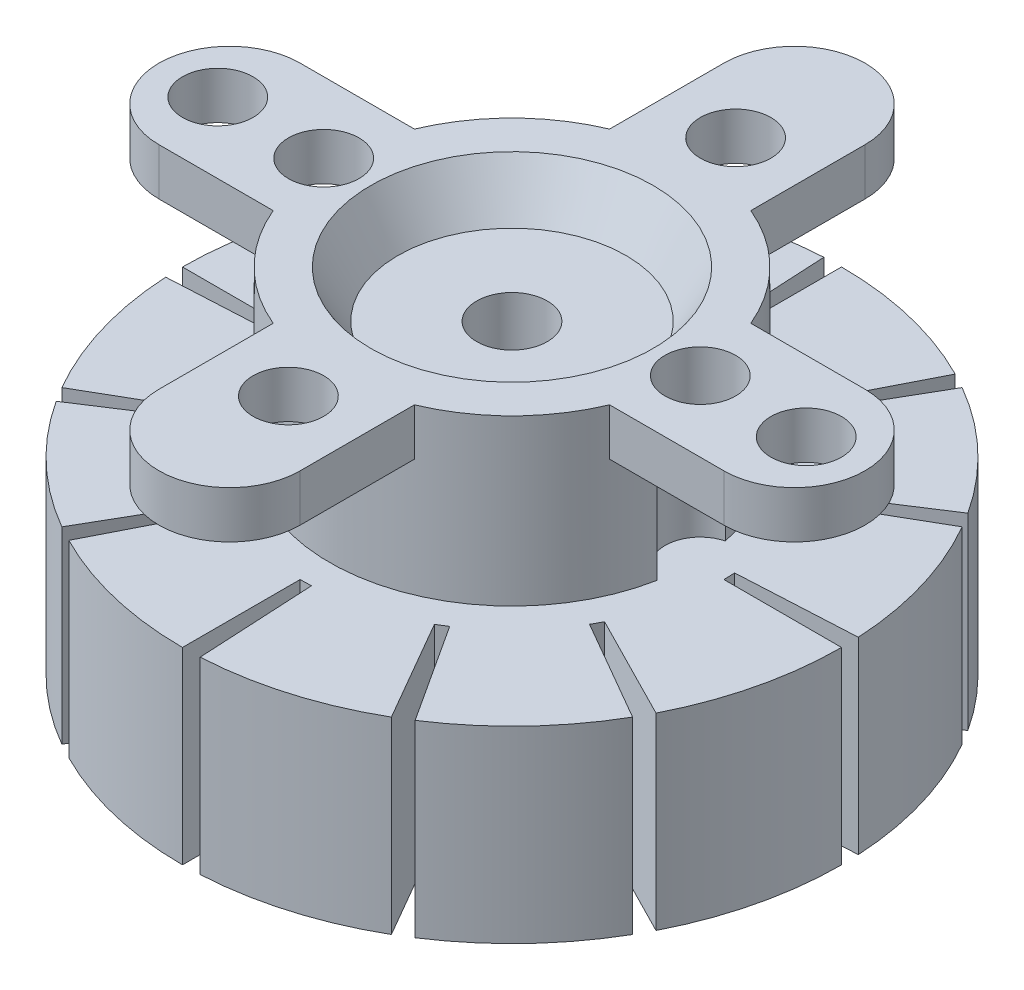
SolidWorks part; units mm, degrees
material "Custom Plastic"
ref_plane "Front Plane" through (0, 0, 0) normal (0, 0, 1) x (1, 0, 0)
ref_plane "Top Plane" through (0, 0, 0) normal (0, 1, 0) x (1, 0, 0)
ref_plane "Right Plane" through (0, 0, 0) normal (1, 0, 0) x (0, 0, -1)
sketch "Sketch1" plane through (0, 0, 0) normal (0, 1, 0) x (1, 0, 0)
  line L0 (0, -12) -> (0, 12) construction
  line L1 (-3, -12) -> (-3, 12)
  line L2 (3, -12) -> (3, 12)
  line L3 (-12, 0) -> (12, 0) construction
  line L4 (-12, 3) -> (12, 3)
  line L5 (-12, -3) -> (12, -3)
  arc A0 (-3, -12) -> (3, -12) centre (0, -12) ccw
  arc A1 (3, 12) -> (-3, 12) centre (0, 12) ccw
  arc A2 (-12, 3) -> (-12, -3) centre (-12, 0) ccw
  arc A3 (12, -3) -> (12, 3) centre (12, 0) ccw
  circle A4 centre (0, 0) radius 7.75
  point P2 (0, 0)
  point P13 (0, 0)
  point P18 (0, 0)
  dimension "D2" = 3
  dimension "D4" = 15.5
  dimension "D1" = 24
  dimension "D3" = 2
extrude "Boss-Extrude1" add sketch "Sketch1" along normal blind 2 contours A4 L4 A2 L5 | L4 A4 L5 L1 | L2 A4 L5 | L1 A4 L2 L5 | L5 A4 L1 | L1 A4 L4 | L2 A4 L1 L4 | A4 L2 A1 L1 | L1 L5 L2 L4 | L5 A4 L4 L2 | L4 A4 L2 | A4 L5 A3 L4 | A4 L1 A0 L2
sketch "Sketch2" plane through (0, 2, 0) normal (0, 1, 0) x (1, 0, 0)
  line L0 (0, 0) -> (0, 4.8441) construction
  line L1 (0, 0) -> (-4.7438, 0) construction
  circle A1 centre (8, 0) radius 1.5
  circle A2 centre (12.5, 0) radius 1.5
  circle A3 centre (0, 9.5) radius 1.5
  circle A4 centre (0, -9.5) radius 1.5
  circle A5 centre (-12.5, 0) radius 1.5
  circle A6 centre (-8, 0) radius 1.5
  dimension "D1" = 12.5
  dimension "D2" = 3
  dimension "D3" = 9.5
  dimension "D4" = 8
extrude "Cut-Extrude1" cut sketch "Sketch2" against normal through all
sketch "Sketch3" plane through (0, 2, 0) normal (0, 1, 0) x (1, 0, 0)
  circle A0 centre (0, 0) radius 6
  dimension "D1" = 12
extrude "Cut-Extrude2" cut sketch "Sketch3" against normal through all draft 30
sketch "Sketch4" plane through (0, 0, 0) normal (0, -1, 0) x (1, 0, 0)
  arc A0 (-7.6133, -1.4493) -> (7.6133, -1.4493) centre (0, 0) ccw
  circle A1 centre (-8, 0) radius 1.5 construction
  circle A2 centre (8, 0) radius 1.5 construction
  arc A3 (-7.6133, -1.4493) -> (-7.6133, 1.4493) centre (-8, 0) ccw
  arc A4 (7.6133, 1.4493) -> (7.6133, -1.4493) centre (8, 0) ccw
  arc A5 (7.6133, 1.4493) -> (-7.6133, 1.4493) centre (0, 0) ccw
  dimension "D1" = 15.5
extrude "Boss-Extrude2" add sketch "Sketch4" along normal blind 13
sketch "Sketch5" plane through (0, -13, 0) normal (0, -1, 0) x (1, 0, 0)
  circle A0 centre (0, 0) radius 14
  dimension "D1" = 28
extrude "Boss-Extrude3" add sketch "Sketch5" against normal blind 8
sketch "Sketch6" plane through (0, 0, 0) normal (0, 1, 0) x (1, 0, 0)
  circle A0 centre (0, 0) radius 1.5
  dimension "D1" = 3
extrude "Cut-Extrude3" cut sketch "Sketch6" against normal through all
sketch "Sketch7" plane through (0, -13, 0) normal (0, -1, 0) x (1, 0, 0)
  line L0 (9, 0) -> (14, 0)
  line L1 (8.9877, -0.471) -> (13.9808, -0.7327)
  arc A0 (8.9877, -0.471) -> (9, 0) centre (0, 0) ccw
  circle A1 centre (0, 0) radius 14 construction
  circle A3 centre (0, 0) radius 14
  circle A4 centre (0, 0) radius 14
  dimension "D1" = 5
  dimension "D2" = 3
  dimension "D3" = 5
  dimension "D4" = 4.9931
  dimension "D5" = 0
extrude "Cut-Extrude5" cut sketch "Sketch7" against normal blind 8 contours L0 A0 L1
pattern_circular "CirPattern1" count 12 over 360 about axis through (0, -13, 0) along (0, -1, 0) of "Cut-Extrude5"
